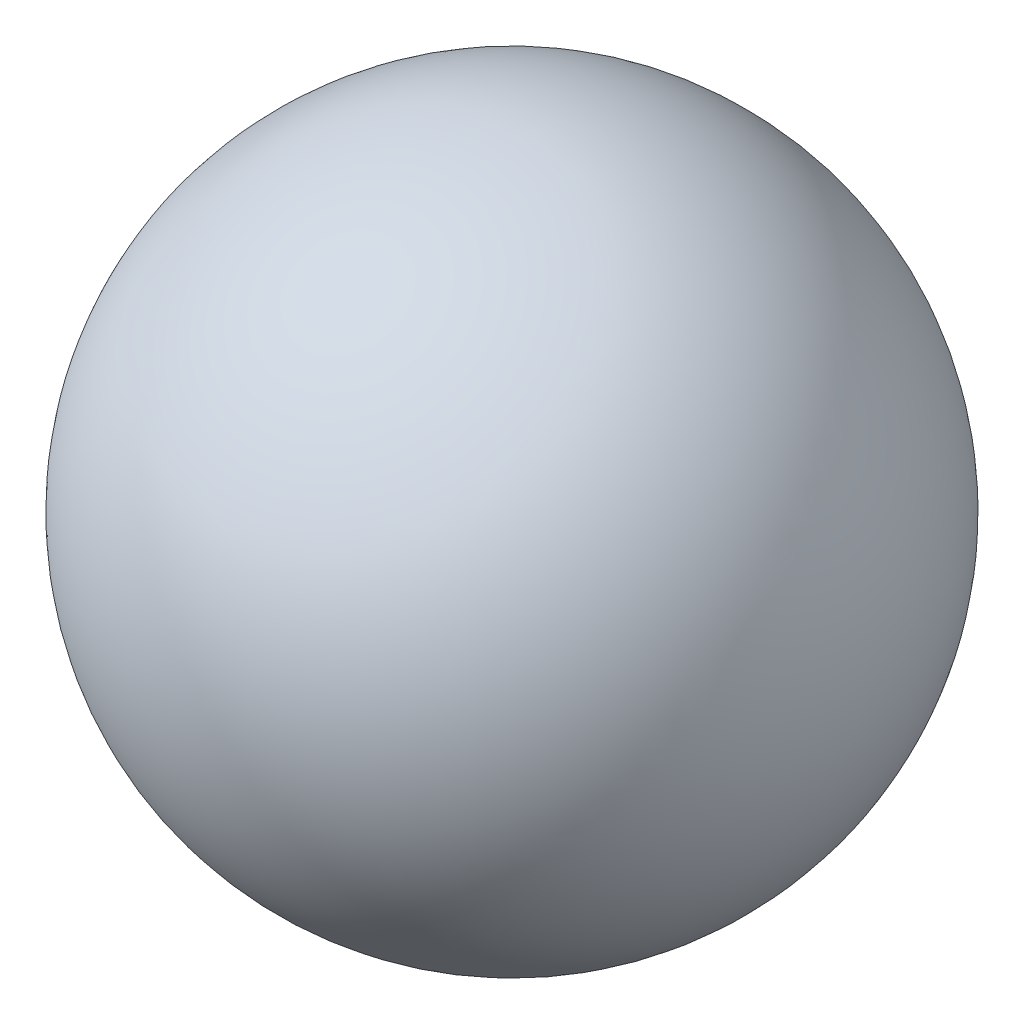
SolidWorks part; units mm, degrees
ref_plane "Front Plane" through (0, 0, 0) normal (0, 0, 1) x (1, 0, 0)
ref_plane "Top Plane" through (0, 0, 0) normal (0, 1, 0) x (1, 0, 0)
ref_plane "Right Plane" through (0, 0, 0) normal (1, 0, 0) x (0, 0, -1)
sketch "Sketch1" plane through (0, 0, 0) normal (0, 0, 1) x (1, 0, 0)
  line L0 (-7.9375, 0) -> (7.9375, 0) construction
  point P4 (0, 0)
  dimension "Diameter" = 15.875
sketch "Sketch3" plane through (0, 0, 0) normal (0, 0, 1) x (1, 0, 0)
  line L0 (-7.9375, 0) -> (7.9375, 0)
  arc A1 (7.9375, 0) -> (-7.9375, 0) centre (0, 0) ccw
revolve "Revolve1" add sketch "Sketch3" angle 360 about L0
